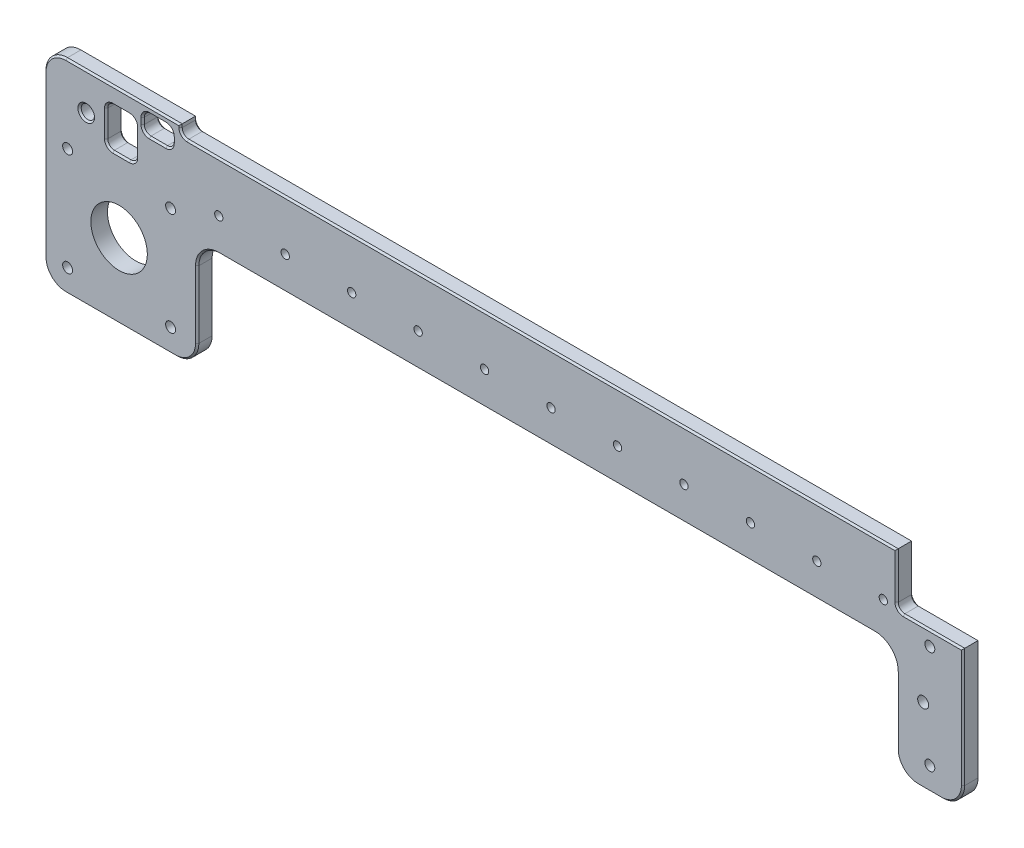
SolidWorks part; units mm, degrees
material "Cast Alloy Steel"
ref_plane "Front plane" through (0, 0, 0) normal (0, 0, 1) x (1, 0, 0)
ref_plane "Top plane" through (0, 0, 0) normal (0, 1, 0) x (1, 0, 0)
ref_plane "Right Plane" through (0, 0, 0) normal (1, 0, 0) x (0, 0, -1)
sketch "Sketch1" plane through (0, 0, 0) normal (0, 0, 1) x (1, 0, 0)
  line L0 (-14.5, -5.2462) -> (-45.5, -5.2462) construction
  line L3 (0, -10) -> (197.5, -10)
  line L5 (-45.5, -5.2462) -> (-45.5, -36.2462) construction
  line L7 (-52.5, 11.5) -> (-52.5, -36.7462)
  line L8 (-46, -43.2462) -> (-13, -43.2462)
  line L9 (-6.5, -36.7462) -> (-6.5, -16.5)
  line L11 (204, -16.5) -> (204, -36.7462)
  line L12 (210.5, -43.2462) -> (217.5, -43.2462)
  line L13 (224, -36.7462) -> (224, -0.9462)
  line L17 (0, 0) -> (20, 0) construction
  line L18 (-46, 18) -> (-11.5, 18)
  line L22 (-30, -14) -> (-30, 0) construction
  line L26 (204, 15) -> (-9.5, 15)
  line L27 (-11.5, 18) -> (-11.5, 17)
  line L29 (-20.9, 16) -> (-15.9, 16)
  line L30 (-22.9, 14) -> (-22.9, 12.12)
  line L31 (-20.9, 10.12) -> (-15.9, 10.12)
  line L32 (-13.9, 14) -> (-13.9, 12.12)
  line L34 (204, 15) -> (204, 1.0538)
  line L35 (206, -0.9462) -> (224, -0.9462)
  line L37 (-26.9, 12.9) -> (-31.9, 12.9)
  line L38 (-24.9, 10.9) -> (-24.9, 2.9)
  line L39 (-26.9, 0.9) -> (-31.9, 0.9)
  line L40 (-33.9, 10.9) -> (-33.9, 2.9)
  circle A0 centre (0, 0) radius 1.25
  circle A1 centre (20, 0) radius 1.25
  circle A2 centre (40, 0) radius 1.25
  circle A3 centre (60, 0) radius 1.25
  circle A4 centre (80, 0) radius 1.25
  circle A5 centre (100, 0) radius 1.25
  circle A6 centre (120, 0) radius 1.25
  circle A7 centre (140, 0) radius 1.25
  circle A8 centre (160, 0) radius 1.25
  circle A9 centre (180, 0) radius 1.25
  circle A12 centre (-30, -20.7462) radius 8.5
  circle A13 centre (-45.5, -5.2462) radius 1.5
  circle A14 centre (-14.5, -5.2462) radius 1.5
  circle A15 centre (-45.5, -36.2462) radius 1.5
  circle A16 centre (-14.5, -36.2462) radius 1.5
  arc A19 (-13, -43.2462) -> (-6.5, -36.7462) centre (-13, -36.7462) ccw
  arc A20 (0, -10) -> (-6.5, -16.5) centre (0, -16.5) ccw
  arc A22 (197.5, -10) -> (204, -16.5) centre (197.5, -16.5) cw
  arc A23 (204, -36.7462) -> (210.5, -43.2462) centre (210.5, -36.7462) ccw
  arc A24 (217.5, -43.2462) -> (224, -36.7462) centre (217.5, -36.7462) ccw
  circle A42 centre (-30, -20.7462) radius 6.3662 construction
  circle A43 centre (-30, -20.7462) radius 6.7462 construction
  arc A45 (-46, 18) -> (-52.5, 11.5) centre (-46, 11.5) ccw
  arc A46 (-15.9, 16) -> (-13.9, 14) centre (-15.9, 14) cw
  arc A47 (-15.9, 10.12) -> (-13.9, 12.12) centre (-15.9, 12.12) ccw
  arc A48 (-22.9, 12.12) -> (-20.9, 10.12) centre (-20.9, 12.12) ccw
  arc A49 (-20.9, 16) -> (-22.9, 14) centre (-20.9, 14) ccw
  circle A50 centre (200, 0) radius 1.25
  arc A52 (-46, -43.2462) -> (-52.5, -36.7462) centre (-46, -36.7462) cw
  circle A54 centre (212, -20.7462) radius 1.65
  circle A55 centre (214, -36.2462) radius 1.5
  arc A56 (204, 1.0538) -> (206, -0.9462) centre (206, 1.0538) ccw
  circle A57 centre (214, -5.2462) radius 1.5
  arc A58 (-9.5, 15) -> (-11.5, 17) centre (-9.5, 17) cw
  arc A59 (-26.9, 12.9) -> (-24.9, 10.9) centre (-26.9, 10.9) cw
  arc A60 (-31.9, 12.9) -> (-33.9, 10.9) centre (-31.9, 10.9) ccw
  arc A61 (-31.9, 0.9) -> (-33.9, 2.9) centre (-31.9, 2.9) cw
  arc A62 (-24.9, 2.9) -> (-26.9, 0.9) centre (-26.9, 2.9) cw
  circle A63 centre (-39.9, 6.9) radius 2
  point P37 (-45.5, -20.7462)
  point P43 (-30, -5.2462)
  point P84 (214, -43.2462)
  point P89 (-24.9, 6.9)
  point P90 (-29.4, 0.9)
  point P93 (-24.9, 12.9)
  point P101 (-33.9, 0.9)
  point P104 (-24.9, 0.9)
  point P108 (-33.9, 6.9)
  dimension "D3" = 2.5
  dimension "D9" = 17
  dimension "D10" = 12.7324
  dimension "D18" = 2
  dimension "D4" = 6.5
  dimension "D38" = 2
  dimension "D6" = 3
  dimension "D31" = 3.3
  dimension "D39" = 4
  dimension "D2" = 20
  dimension "D5" = 10
  dimension "D8" = 31
  dimension "D11" = 30
  dimension "D14" = 20
  dimension "D15" = 18
  dimension "D21" = 0.38
  dimension "D22" = 14
  dimension "D16" = 3
  dimension "D17" = 41
  dimension "D19" = 5.88
  dimension "D20" = 9
  dimension "D24" = 29.6
  dimension "D12" = 210.5
  dimension "D25" = 7
  dimension "D26" = 7
  dimension "D27" = 46
  dimension "D30" = 22.5
  dimension "D32" = 7
  dimension "D7" = 20
  dimension "D34" = 31
  dimension "D23" = 2
  dimension "D28" = 9
  dimension "D35" = 12
  dimension "D36" = 11.1
  dimension "D37" = 23.1
  dimension "D33" = 6
  dimension "D29" = 242
  dimension "D13" = 42.3
  dimension "D1" = 11
extrude "Boss-Extrude1" add sketch "Sketch1" along normal blind 5
chamfer "Chamfer1" distance 0.5 angle 45 76 edges at (98.75, -10, 0) (-4.5962, -11.9038, 0) (-6.5, -26.6231, 0) (-8.4038, -41.3424, 0) (-29.5, -43.2462, 0) (-52.5, -12.6231, 0) (98.75, -10, 5) (-4.5962, -11.9038, 5) (-6.5, -26.6231, 5) (-8.4038, -41.3424, 5) (-29.5, -43.2462, 5) (-52.5, -12.6231, 5) (224, -18.8462, 0) (222.0962, -41.3424, 0) (214, -43.2462, 0) (205.9038, -41.3424, 0) (204, -26.6231, 0) (202.0962, -11.9038, 0) (224, -18.8462, 5) (222.0962, -41.3424, 5) (214, -43.2462, 5) (205.9038, -41.3424, 5) (204, -26.6231, 5) (202.0962, -11.9038, 5) (-28.75, 18, 0) (-28.75, 18, 5) (-50.5962, 16.0962, 0) (-50.5962, 16.0962, 5) (-11.5, 17.5, 0) (97.25, 15, 0) (-11.5, 17.5, 5) (97.25, 15, 5) (-18.4, 16, 5) (-22.3142, 15.4142, 5) (-14.4858, 15.4142, 5) (-22.9, 13.06, 5) (-13.9, 13.06, 5) (-22.3142, 10.7058, 5) (-14.4858, 10.7058, 5) (-18.4, 10.12, 5) (-18.4, 16, 0) (-22.3142, 15.4142, 0) (-14.4858, 15.4142, 0) (-22.9, 13.06, 0) (-13.9, 13.06, 0) (-22.3142, 10.7058, 0) (-14.4858, 10.7058, 0) (-18.4, 10.12, 0) (-50.5962, -41.3424, 0) (-50.5962, -41.3424, 5) (-10.9142, 15.5858, 0) (-10.9142, 15.5858, 5) (204, 8.0269, 5) (204.5858, -0.3604, 5) (215, -0.9462, 5) (215, -0.9462, 0) (204.5858, -0.3604, 0) (204, 8.0269, 0) (-29.4, 12.9, 0) (-33.3142, 12.3142, 0) (-25.4858, 12.3142, 0) (-33.9, 6.9, 0) (-24.9, 6.9, 0) (-33.3142, 1.4858, 0) (-25.4858, 1.4858, 0) (-29.4, 0.9, 0) (-29.4, 12.9, 5) (-33.3142, 12.3142, 5) (-25.4858, 12.3142, 5) (-33.9, 6.9, 5) (-24.9, 6.9, 5) (-33.3142, 1.4858, 5) (-25.4858, 1.4858, 5) (-29.4, 0.9, 5) (-37.9, 6.9, 5) (-37.9, 6.9, 0)
equation "\"D10@Sketch1\"=40/pi"
